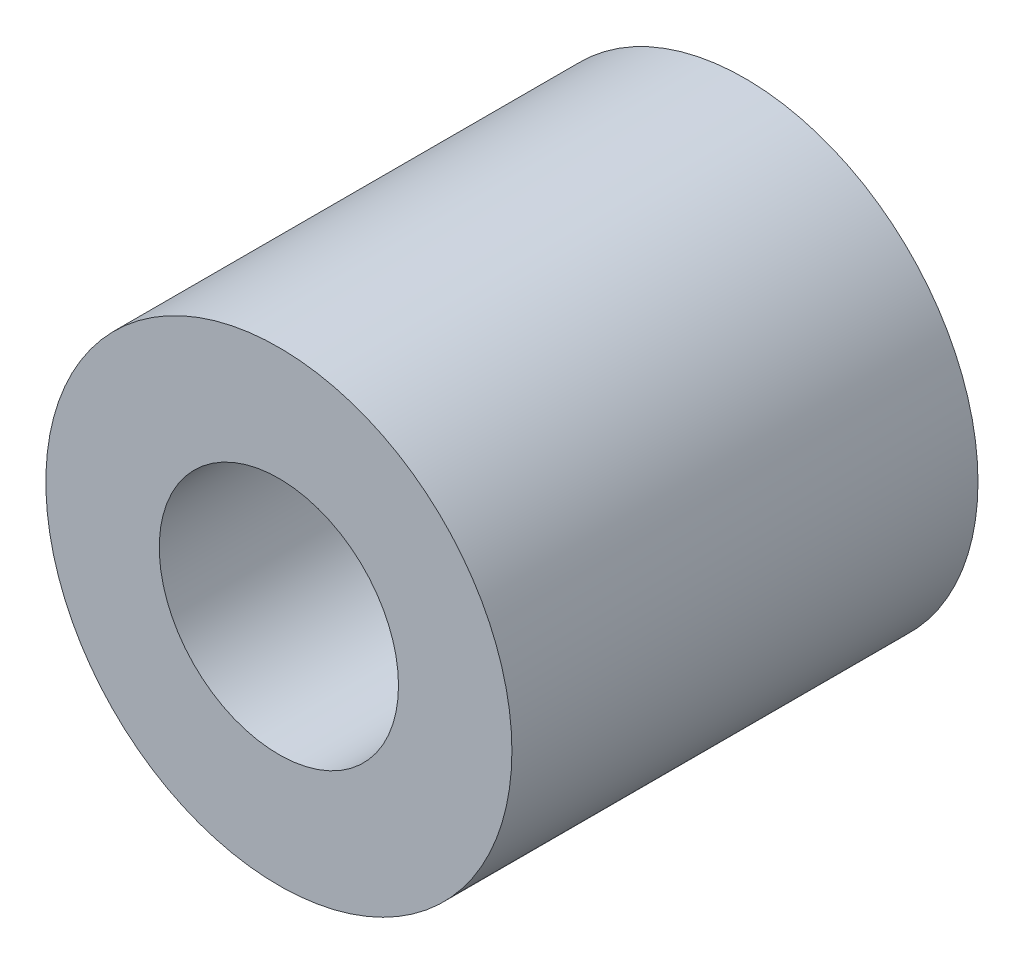
SolidWorks part; units mm, degrees
ref_plane "Plan de face" through (0, 0, 0) normal (0, 0, 1) x (1, 0, 0)
ref_plane "Plan de dessus" through (0, 0, 0) normal (0, 1, 0) x (1, 0, 0)
ref_plane "Plan de droite" through (0, 0, 0) normal (1, 0, 0) x (0, 0, -1)
sketch "Esquisse1" plane through (0, 0, 0) normal (0, 0, 1) x (1, 0, 0)
  circle A0 centre (0, 0) radius 3
  circle A1 centre (0, 0) radius 1.54
extrude "Extrusion1" add sketch "Esquisse1" along normal blind 6
